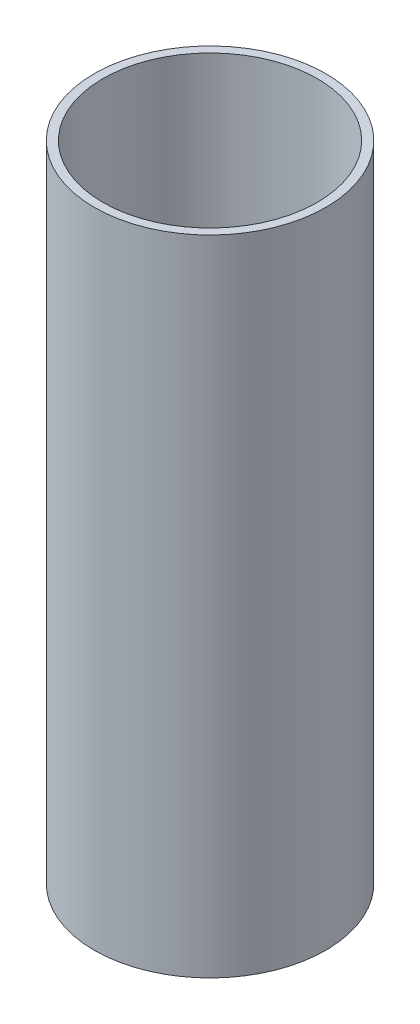
SolidWorks part; units mm, degrees
ref_plane "Front Plane" through (0, 0, 0) normal (0, 0, 1) x (1, 0, 0)
ref_plane "Top Plane" through (0, 0, 0) normal (0, 1, 0) x (1, 0, 0)
ref_plane "Right Plane" through (0, 0, 0) normal (1, 0, 0) x (0, 0, -1)
sketch "Sketch1" plane through (0, 0, 0) normal (0, 1, 0) x (1, 0, 0)
  circle A0 centre (0, 0) radius 27
  circle A1 centre (0, 0) radius 25
  dimension "D1" = 54
  dimension "D2" = 50
extrude "Boss-Extrude1" add sketch "Sketch1" along normal blind 150
